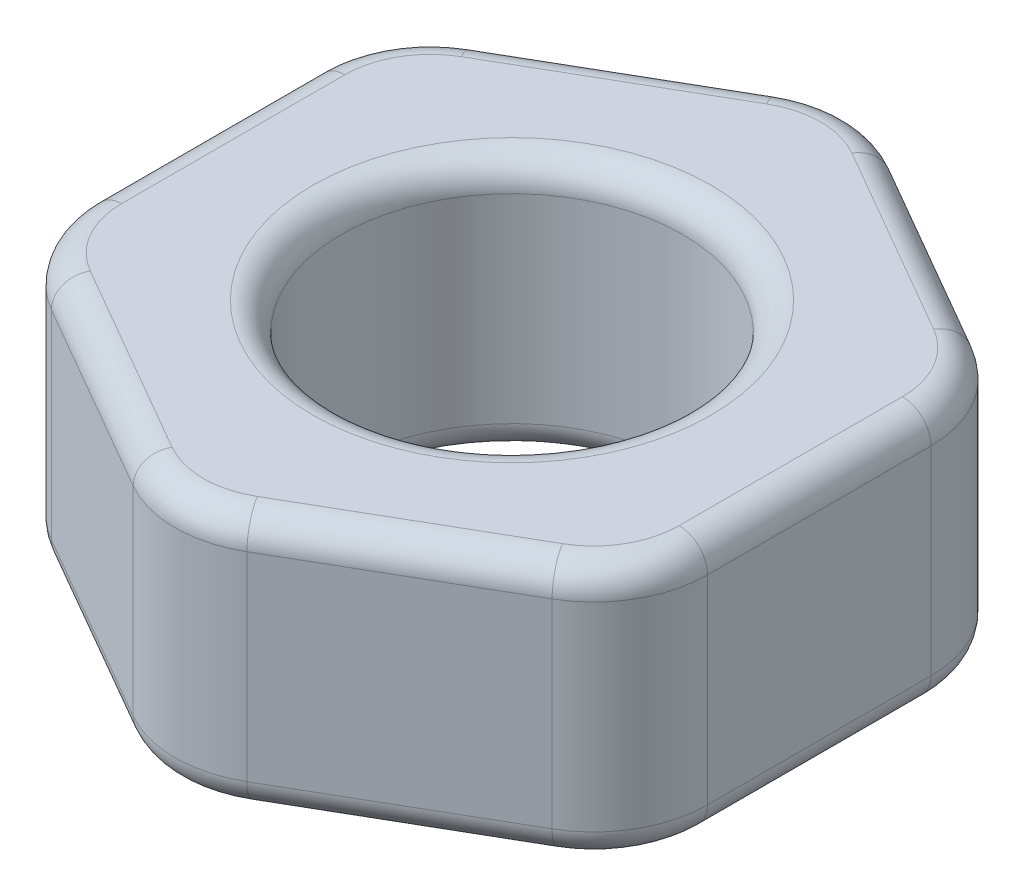
SolidWorks part; units mm, degrees
ref_plane "Front Plane" through (0, 0, 0) normal (0, 0, 1) x (1, 0, 0)
ref_plane "Top Plane" through (0, 0, 0) normal (0, 1, 0) x (1, 0, 0)
ref_plane "Right Plane" through (0, 0, 0) normal (1, 0, 0) x (0, 0, -1)
sketch "Sketch1" plane through (0, 0, 0) normal (0, 1, 0) x (1, 0, 0)
  line L1 (2.7, -1.5588) -> (2.7, 1.5588)
  line L2 (2.7, 1.5588) -> (0, 3.1177)
  line L3 (0, 3.1177) -> (-2.7, 1.5588)
  line L4 (-2.7, 1.5588) -> (-2.7, -1.5588)
  line L5 (-2.7, -1.5588) -> (0, -3.1177)
  line L6 (0, -3.1177) -> (2.7, -1.5588)
  circle A0 centre (0, 0) radius 1.5
  circle A1 centre (0, 0) radius 2.7 construction
  dimension "D2" = 3
  dimension "D1" = 5.4
extrude "Boss-Extrude1" add sketch "Sketch1" along normal blind 2.25
fillet "Fillet1" radius 1 6 edges at (0, 1.125, -3.1177) (-2.7, 1.125, -1.5588) (-2.7, 1.125, 1.5588) (2.7, 1.125, -1.5588) (2.7, 1.125, 1.5588) (0, 1.125, 3.1177)
fillet "Fillet2" radius 0.25 26 edges at (0, 0, 1.5) (-2.566, 0, -1.4815) (-2.7, 0, 0) (-2.566, 0, 1.4815) (-1.35, 0, 2.3383) (0, 0, 2.963) (1.35, 0, 2.3383) (2.566, 0, 1.4815) (2.7, 0, 0) (2.566, 0, -1.4815) (1.35, 0, -2.3383) (0, 0, -2.963) (-1.35, 0, -2.3383) (0, 2.25, 1.5) (2.566, 2.25, -1.4815) (2.7, 2.25, 0) (2.566, 2.25, 1.4815) (1.35, 2.25, 2.3383) (0, 2.25, 2.963) (-1.35, 2.25, 2.3383) (-2.566, 2.25, 1.4815) (-2.7, 2.25, 0) (-2.566, 2.25, -1.4815) (-1.35, 2.25, -2.3383) (0, 2.25, -2.963) (1.35, 2.25, -2.3383)
